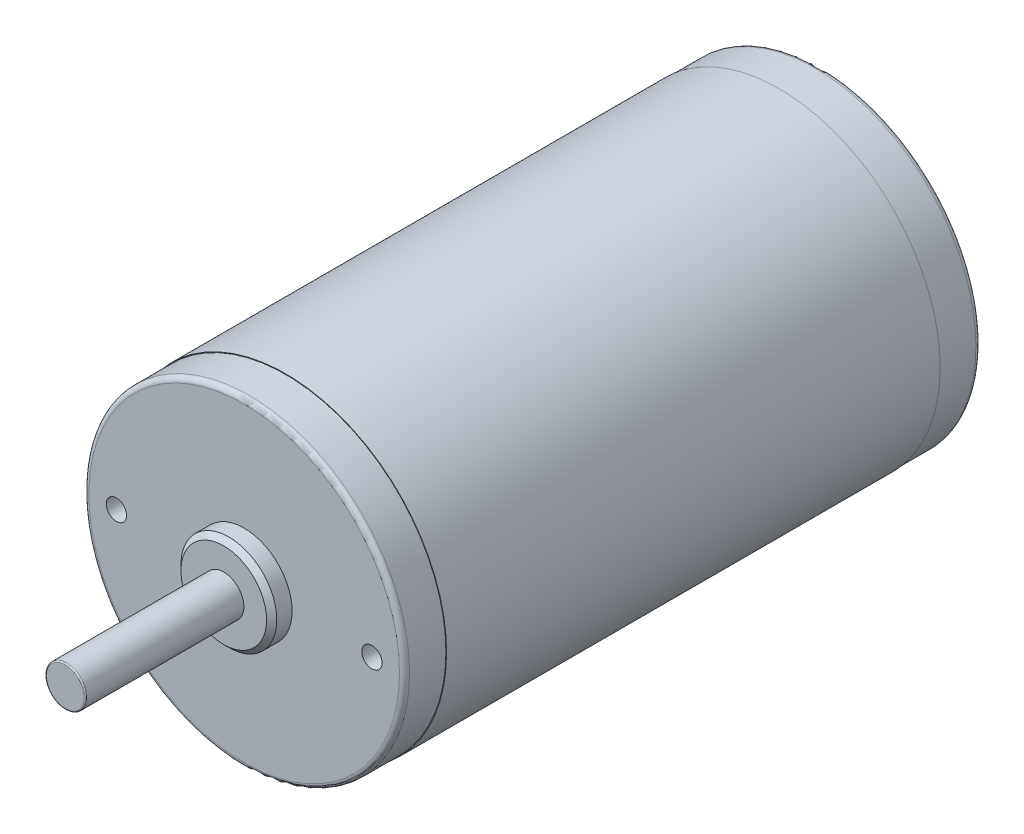
SolidWorks part; units mm, degrees
ref_plane "Front Plane" through (0, 0, 0) normal (0, 0, 1) x (1, 0, 0)
ref_plane "Top Plane" through (0, 0, 0) normal (0, 1, 0) x (1, 0, 0)
ref_plane "Right Plane" through (0, 0, 0) normal (1, 0, 0) x (0, 0, -1)
ref_plane "Plane1" through (0, 109.2962, 0) normal (0, -1, 0) x (1, 0, 0)
sketch "Sketch1" plane through (0, 109.2962, 0) normal (0, -1, 0) x (1, 0, 0)
  line L0 (67.564, 10.8204) -> (35.56, 10.8204)
  line L1 (35.56, 10.8204) -> (35.56, -87.3252)
  line L2 (35.56, -87.3252) -> (67.564, -87.3252)
  line L3 (67.564, -87.3252) -> (67.564, 10.8204)
  line L4 (35.56, 10.8204) -> (35.56, -87.3252) construction
revolve "Revolve1" add sketch "Sketch1" angle 360 about L4
sketch "Sketch2" plane through (0, 0, 10.8204) normal (0, 0, 1) x (1, 0, 0)
  circle A0 centre (35.56, 109.2962) radius 31.877
extrude "Boss-Extrude1" add sketch "Sketch2" along normal blind 8.2296
ref_plane "Plane2" through (0, 0, 18.542) normal (0, 0, -1) x (-1, 0, 0)
sketch "Sketch5" plane through (0, 0, 18.542) normal (0, 0, -1) x (-1, 0, 0)
  circle A0 centre (-35.56, 109.2962) radius 9.525
extrude "Boss-Extrude2" add sketch "Sketch5" against normal blind 4.572
sketch "Sketch6" plane through (0, 0, 23.114) normal (0, 0, 1) x (1, 0, 0)
  circle A0 centre (35.56, 109.2962) radius 4
extrude "Boss-Extrude3" add sketch "Sketch6" along normal blind 31.5
sketch "Sketch8" plane through (0, 0, -87.3252) normal (0, 0, -1) x (-1, 0, 0)
  circle A0 centre (-35.56, 109.2962) radius 31.877
extrude "Boss-Extrude4" add sketch "Sketch8" along normal blind 8.2296
sketch "Sketch9" plane through (0, 0, -95.5548) normal (0, 0, -1) x (-1, 0, 0)
  circle A0 centre (-35.56, 109.2962) radius 15.0368
extrude "Boss-Extrude5" add sketch "Sketch9" along normal blind 4.7625
ref_plane "Plane3" [suppressed] through (0, 120.5036, 0) normal (0, 1, 0) x (-1, 0, 0)
sketch "Sketch10" [suppressed] plane through (0, 120.5036, 0) normal (0, 1, 0) x (-1, 0, 0)
  line L0 (-56.2851, -97.8027) -> (-54.1671, -97.8027)
  line L1 (-54.1671, -97.8027) -> (-54.1671, -95.5548)
  line L2 (-54.1671, -95.5548) -> (-58.4851, -95.5548)
  line L3 (-58.4851, -95.5548) -> (-58.4851, -95.6027)
  line L4 (-58.4851, -95.6027) -> (-56.2851, -97.8027)
  line L5 (-54.1671, -97.8027) -> (-54.1671, -95.5548) construction
revolve "Revolve2" [suppressed] add sketch "Sketch10" angle 360 about L5
ref_plane "Plane4" [suppressed] through (0, 127.9033, 0) normal (0, 1, 0) x (-1, 0, 0)
sketch "Sketch11" [suppressed] plane through (0, 127.9033, 0) normal (0, 1, 0) x (-1, 0, 0)
  line L0 (-48.8854, -97.8027) -> (-46.7674, -97.8027)
  line L1 (-46.7674, -97.8027) -> (-46.7674, -95.5548)
  line L2 (-46.7674, -95.5548) -> (-51.0854, -95.5548)
  line L3 (-51.0854, -95.5548) -> (-51.0854, -95.6027)
  line L4 (-51.0854, -95.6027) -> (-48.8854, -97.8027)
  line L5 (-46.7674, -97.8027) -> (-46.7674, -95.5548) construction
revolve "Revolve3" [suppressed] add sketch "Sketch11" angle 360 about L5
hole_wizard "Hole2" positions "Sketch13" profile "Sketch12" legacy
sketch "Sketch13" plane through (0, 0, 19.05) normal (0, 0, 1) x (1, 0, 0)
  point P0 (60.96, 109.2962)
sketch "Sketch12" plane through (60.96, 109.2962, 19.05) normal (1, 0, 0) x (0, -1, 0)
  line L0 (0, 0) -> (0, 14.8277)
  line L1 (0, 14.8277) -> (2.0193, 13.6144)
  line L2 (2.0193, 13.6144) -> (2.0193, 0)
  line L4 (2.0193, 0) -> (0, 0)
  line L6 (0, 14.8277) -> (-2.0193, 13.6144) construction
  line L7 (0, -4.2442) -> (0, 117.3081) construction
  dimension "Diameter" = 4.0386
  dimension "Depth" = 13.6144
  dimension "Drill Angle" = 118
hole_wizard "Hole3" positions "Sketch15" profile "Sketch14" legacy
sketch "Sketch15" plane through (0, 0, 19.05) normal (0, 0, 1) x (1, 0, 0)
  point P0 (10.16, 109.2962)
sketch "Sketch14" plane through (10.16, 109.2962, 19.05) normal (1, 0, 0) x (0, -1, 0)
  line L0 (0, 0) -> (0, 14.8277)
  line L1 (0, 14.8277) -> (2.0193, 13.6144)
  line L2 (2.0193, 13.6144) -> (2.0193, 0)
  line L4 (2.0193, 0) -> (0, 0)
  line L6 (0, 14.8277) -> (-2.0193, 13.6144) construction
  line L7 (0, -4.2442) -> (0, 117.3081) construction
  dimension "Diameter" = 4.0386
  dimension "Depth" = 13.6144
  dimension "Drill Angle" = 118
chamfer "Chamfer1" distance 1.016 angle 45 1 edges at (45.085, 109.2962, 23.114)
fillet "Fillet1" radius 0.254 1 edges at (39.56, 109.2962, 54.614)
fillet "Fillet2" radius 1 1 edges at (3.683, 109.2962, -95.5548)
fillet "Fillet3" radius 1 1 edges at (67.437, 109.2962, 19.05)
fillet "Fillet4" radius 1 1 edges at (20.5232, 109.2962, -100.3173)
ref_plane "Plane5" [suppressed] through (39.56, 0, 0) normal (1, 0, 0) x (0, 0, -1)
sketch "Sketch16" [suppressed] plane through (39.56, 0, 0) normal (1, 0, 0) x (0, 0, -1)
  line L0 (-26.05, 109.2962) -> (-23.114, 109.2962)
  line L1 (-26.05, 110.3462) -> (-46.15, 110.3462)
  line L2 (-26.05, 110.3462) -> (-26.05, 108.2462)
  line L3 (-26.05, 108.2462) -> (-46.15, 108.2462)
  line L4 (-46.15, 110.3462) -> (-46.15, 108.2462)
  line L5 (-23.114, 113.2962) -> (-23.114, 105.2962) construction
  line L6 (-19.05, 140.1732) -> (-19.05, 78.4192) construction
  dimension "D1" = 7
  dimension "D2" = 2.1
  dimension "D3" = 20.1
extrude "Cut-Extrude2" [suppressed] cut sketch "Sketch16" against normal blind 1.2 contours L1 L4 L3 L2
fillet "Fillet5" [suppressed] radius 1.05
